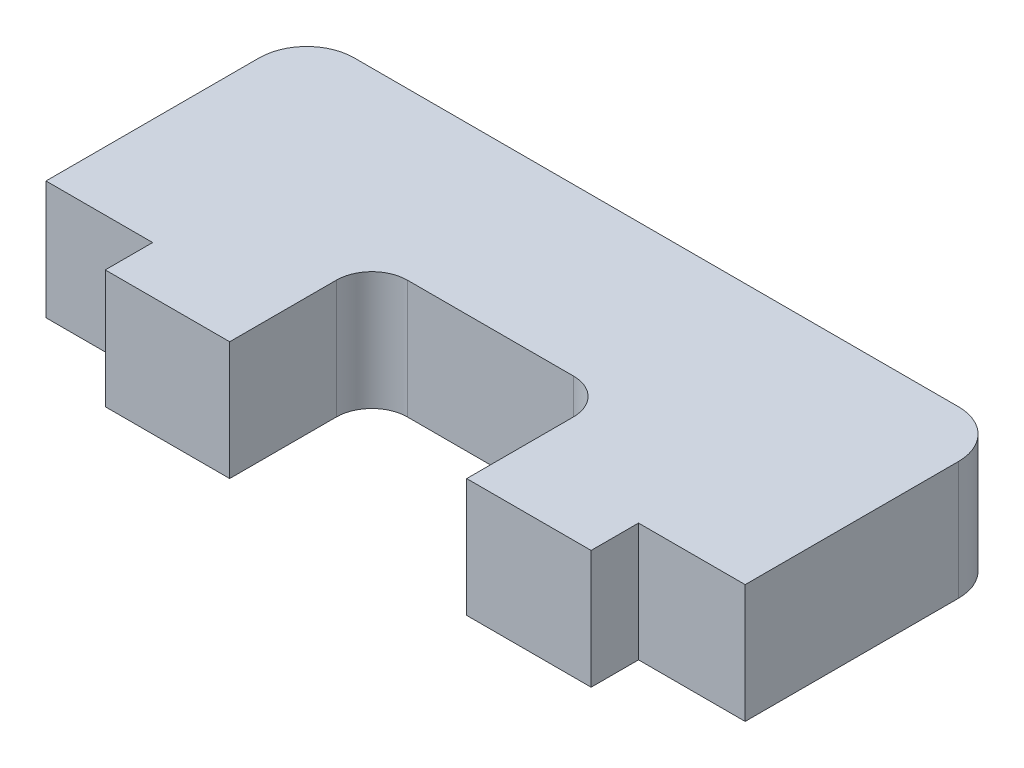
SolidWorks part; units mm, degrees
ref_plane "Front Plane" through (0, 0, 0) normal (0, 0, 1) x (1, 0, 0)
ref_plane "Top Plane" through (0, 0, 0) normal (0, 1, 0) x (1, 0, 0)
ref_plane "Right Plane" through (0, 0, 0) normal (1, 0, 0) x (0, 0, -1)
sketch "Sketch1" plane through (0, 0, 0) normal (0, 1, 0) x (1, 0, 0)
  line L1 (14.75, -6.5) -> (-14.75, -6.5)
  line L2 (14.75, -6.5) -> (14.75, 6.5)
  line L3 (14.75, 6.5) -> (-14.75, 6.5)
  line L4 (-14.75, -6.5) -> (-14.75, 6.5)
  line L5 (14.75, -6.5) -> (-14.75, 6.5) construction
  line L6 (14.75, 6.5) -> (-14.75, -6.5) construction
  point P0 (0, 0)
  dimension "D1" = 13
  dimension "D2" = 29.5
extrude "Boss-Extrude1" add sketch "Sketch1" along normal blind 5
sketch "Sketch2" plane through (0, 5, 0) normal (0, 1, 0) x (1, 0, 0)
  line L0 (-5, -6.5) -> (5, -6.5)
  line L1 (-5, -6.5) -> (-5, -0.5)
  line L2 (5, -6.5) -> (5, -0.5)
  line L3 (-5, -0.5) -> (5, -0.5)
  line L4 (-14.75, -6.5) -> (14.75, -6.5) construction
  point P6 (0, -6.5)
  dimension "D1" = 10
  dimension "D2" = 6
extrude "Cut-Extrude1" cut sketch "Sketch2" against normal through all
fillet "Fillet1" radius 2 2 edges at (14.75, 2.5, -6.5) (-14.75, 2.5, -6.5)
fillet "Fillet2" radius 1.5 2 edges at (5, 2.5, 0.5) (-5, 2.5, 0.5)
sketch "Sketch3" plane through (0, 0, 6.5) normal (0, 0, 1) x (1, 0, 0)
  line L0 (-10.25, 5) -> (-10.25, 0)
  line L1 (-10.25, 5) -> (10.25, 5)
  line L2 (-10.25, 0) -> (10.25, 0)
  line L3 (10.25, 5) -> (10.25, 0)
  line L4 (-14.75, 5) -> (-5, 5) construction
  line L5 (-14.75, 0) -> (-5, 0) construction
  line L6 (-14.75, 5) -> (-14.75, 0) construction
  line L7 (14.75, 5) -> (14.75, 0) construction
  dimension "D1" = 4.5
  dimension "D2" = 4.5
extrude "Cut-Extrude2" cut sketch "Sketch3" against normal blind 2 flip side to cut
